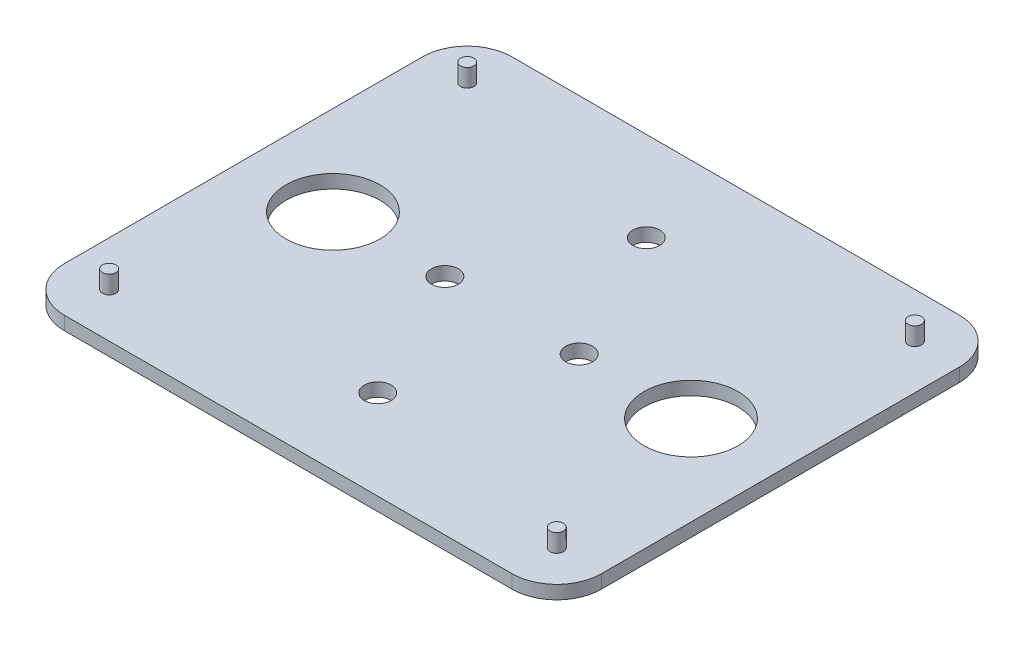
SolidWorks part; units mm, degrees
ref_plane "Plan de face" through (0, 0, 0) normal (0, 0, 1) x (1, 0, 0)
ref_plane "Plan de dessus" through (0, 0, 0) normal (0, 1, 0) x (1, 0, 0)
ref_plane "Plan de droite" through (0, 0, 0) normal (1, 0, 0) x (0, 0, -1)
sketch "Esquisse1" plane through (0, 0, 0) normal (0, 1, 0) x (1, 0, 0)
  line L1 (0, 0) -> (-120, 0)
  line L2 (0, 0) -> (0, 100)
  line L3 (0, 100) -> (-120, 100)
  line L4 (-120, 0) -> (-120, 100)
  dimension "D1" = 120
  dimension "D2" = 100
extrude "Boss.-Extru.1" add sketch "Esquisse1" along normal blind 3
fillet "Congé1" radius 10 4 edges at (-120, 1.5, 0) (0, 1.5, -100) (0, 1.5, 0) (-120, 1.5, -100)
sketch "Esquisse2" plane through (0, 3, 0) normal (0, 1, 0) x (1, 0, 0)
  line L0 (-120, 90) -> (-120, 10) construction
  line L1 (-10, 100) -> (-110, 100) construction
  line L2 (-110, 0) -> (-10, 0) construction
  line L3 (0, 10) -> (0, 90) construction
  circle A0 centre (-110, 90) radius 1.5
  circle A1 centre (-10, 90) radius 1.5
  circle A2 centre (-10, 10) radius 1.5
  circle A3 centre (-110, 10) radius 1.5
  dimension "D1" = 3
  dimension "D6" = 3
  dimension "D9" = 3
  dimension "D10" = 3
  dimension "D2" = 10
  dimension "D3" = 10
  dimension "D4" = 10
  dimension "D5" = 10
  dimension "D7" = 10
  dimension "D8" = 10
  dimension "D11" = 10
  dimension "D12" = 10
extrude "Boss.-Extru.2" add sketch "Esquisse2" along normal blind 4
sketch "Esquisse3" plane through (0, 3, 0) normal (0, 1, 0) x (1, 0, 0)
  line L0 (-10, 100) -> (-110, 100) construction
  line L1 (0, 10) -> (0, 90) construction
  line L2 (-120, 90) -> (-120, 10) construction
  line L3 (-110, 0) -> (-10, 0) construction
  circle A0 centre (-100, 50) radius 10.5
  circle A1 centre (-20, 50) radius 10.5
  circle A2 centre (-75, 50) radius 3
  circle A3 centre (-45, 50) radius 3
  circle A4 centre (-60, 80) radius 3
  circle A5 centre (-60, 20) radius 3
  point P18 (-60, 0)
  dimension "D1" = 21
  dimension "D2" = 21
  dimension "D13" = 6
  dimension "D14" = 6
  dimension "D15" = 6
  dimension "D18" = 6
  dimension "D3" = 50
  dimension "D4" = 50
  dimension "D5" = 20
  dimension "D6" = 20
  dimension "D7" = 50
  dimension "D8" = 50
  dimension "D9" = 25
  dimension "D10" = 25
  dimension "D11" = 60
  dimension "D12" = 60
  dimension "D16" = 20
  dimension "D17" = 20
extrude "Enlèv. mat.-Extru.1" cut sketch "Esquisse3" against normal through all
